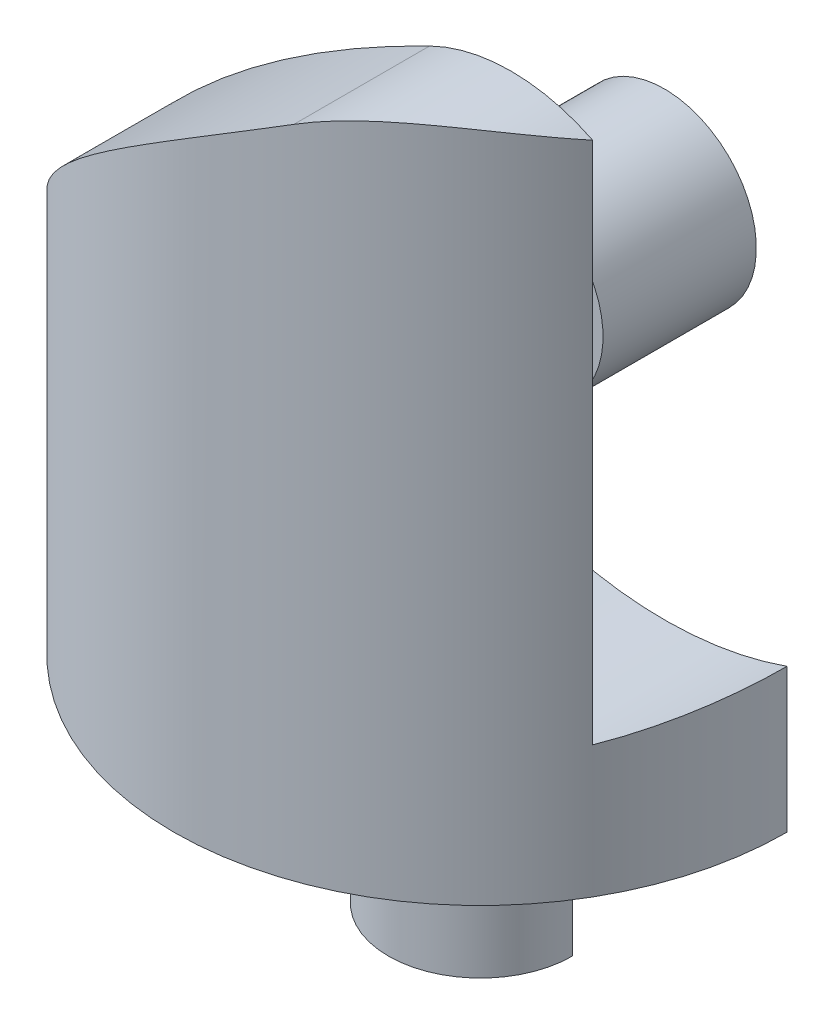
SolidWorks part; units mm, degrees
ref_plane "Front Plane" through (0, 0, 0) normal (0, 0, 1) x (1, 0, 0)
ref_plane "Top Plane" through (0, 0, 0) normal (0, 1, 0) x (1, 0, 0)
ref_plane "Right Plane" through (0, 0, 0) normal (1, 0, 0) x (0, 0, -1)
sketch "Sketch1" plane through (0, 0, 0) normal (0, 1, 0) x (1, 0, 0)
  circle A0 centre (0, 0) radius 5
extrude "Boss-Extrude1" add sketch "Sketch1" along normal blind 13
sketch "Sketch2" plane through (0, 0, 0) normal (0, 0, 1) x (1, 0, 0)
  line L0 (0, 13) -> (3, 13)
  line L1 (-5, 0) -> (5, 0)
  line L2 (-5, 0) -> (-5, 13)
  line L3 (-5, 13) -> (5, 13)
  line L4 (5, 0) -> (5, 13)
  line L5 (3, 13) -> (3, 8)
  line L6 (-5, 0) -> (-5, 3)
  circle A0 centre (3, 8) radius 5
  circle A1 centre (3, 8) radius 3
  spline S0 degree 2 poles (-5, 0) (-5.983, 6.9569) (1.6709, 10.6895) knots 0 0 0 1 1 1
  spline S1 degree 2 poles (5, 0) (4.6919, 3.6204) (5.858, 7.0879) knots 0 0 0 1 1 1
extrude "Cut-Extrude1" cut sketch "Sketch2" against normal through all both and the other way through all contours L2 S0 A0 L0 L3 | A0 S0 A1 L5 | A1 L4 A0 L5 | S1 A0 L4 A1 | A0 L4 L3
sketch "Sketch4" plane through (0, 0, 0) normal (0, 1, 0) x (1, 0, 0)
  line L0 (0, 0) -> (-5.6901, 0)
  line L1 (-5.6901, 0) -> (-5.6901, 7.6833)
  line L2 (-5.6901, 7.6833) -> (11.0269, 8.4961)
  line L3 (11.0269, 8.4961) -> (8.6016, 0)
  line L4 (8.6016, 0) -> (0, 0)
extrude "Cut-Extrude5" cut sketch "Sketch4" against normal through all and the other way through all contours L4 L0 L1 L2 L3
sketch "Sketch5" plane through (0, 0, 0) normal (0, 0, -1) x (-1, 0, 0)
  line L0 (0, 0) -> (0, 3)
  line L1 (0, 3) -> (-6.6708, 3)
  line L2 (-6.6708, 3) -> (-6.6708, 14.95)
  line L3 (-6.6708, 14.95) -> (5.6572, 14.95)
  line L4 (5.6572, 14.95) -> (5.9774, 3)
  line L5 (5.9774, 3) -> (0, 3)
  line M1 (-5, 10.2361) -> (-5, 0)
  spline M4 degree 2 poles (5, 0) (5.983, 6.9569) (-1.6709, 10.6895) knots 0 0 0 1 1 1 only from (5, 3) to (-1.6709, 10.6895)
  arc M5 (-1.6709, 10.6895) -> (-5, 10.2361) centre (-3, 8) ccw
extrude "Cut-Extrude6" cut sketch "Sketch5" against normal blind 2.5 contours L5 L1 M4 M5 M1
sketch "Sketch6" plane through (0, 0, 0) normal (0, 0, -1) x (-1, 0, 0)
  line L0 (0, 0) -> (0, 8)
  line L1 (0, 8) -> (-3, 8)
  circle A0 centre (-3, 8) radius 1.5
extrude "Boss-Extrude2" add sketch "Sketch6" against normal blind 2.5 separate body
sketch "Sketch7" plane through (0, 0, 0) normal (0, -1, 0) x (1, 0, 0)
  line L0 (-1.5, 0) -> (1.5, 0)
  circle A0 centre (0, 0) radius 1.5
  line M1 (-5, 0) -> (5, 0)
extrude "Boss-Extrude3" add sketch "Sketch7" along normal blind 3.5 contours A0 M1
sketch "Sketch8" plane through (0, 0, 0) normal (0, 0, -1) x (-1, 0, 0)
  circle A0 centre (-3, 8) radius 6
  circle A1 centre (-3, 8) radius 1.5
extrude "Cut-Extrude8" cut sketch "Sketch8" against normal blind 2.5
